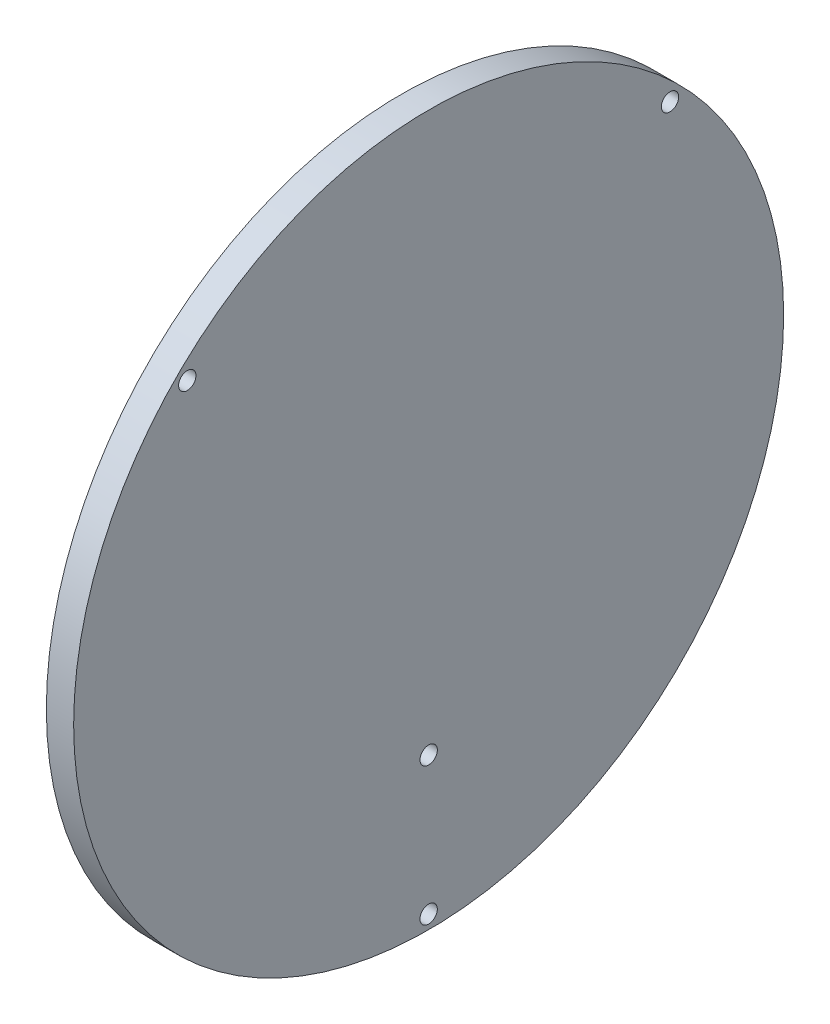
SolidWorks part; units mm, degrees
material "Copper"
ref_plane "Front Plane" through (0, 0, 0) normal (0, 0, 1) x (1, 0, 0)
ref_plane "Top Plane" through (0, 0, 0) normal (0, 1, 0) x (1, 0, 0)
ref_plane "Right Plane" through (0, 0, 0) normal (1, 0, 0) x (0, 0, -1)
sketch "Sketch1" plane through (0, 0, 0) normal (1, 0, 0) x (0, 0, -1)
  circle A0 centre (0, 0) radius 260
extrude "Boss-Extrude1" add sketch "Sketch1" along normal blind 20
ref_plane "Plane1" through (20, 0, 0) normal (1, 0, 0) x (0, 0, -1)
sketch "Sketch2" plane through (20, 0, 0) normal (1, 0, 0) x (0, 0, -1)
  line L0 (0, 260) -> (0, 240)
  line L1 (-260, 0) -> (-240, 0)
  line L2 (183.8478, 183.8478) -> (169.7056, 169.7056)
  line L3 (-183.8478, 183.8478) -> (-169.7056, 169.7056)
  line L4 (169.7056, -169.7056) -> (183.8478, -183.8478)
  line L5 (-169.7056, -169.7056) -> (-183.8478, -183.8478)
  line L6 (0, -240) -> (0, -260)
  line L7 (240, 0) -> (260, 0)
  line L8 (-210.3618, -149.1025) -> (210.3618, -149.1025)
  line L9 (0, 0) -> (0, -149.1025)
  circle A0 centre (0, 3.6977) radius 260
  point P3 (0, -250)
  point P16 (-176.7767, 176.7767)
  point P17 (176.7767, 176.7767)
  point P18 (176.7767, -176.7767)
  point P19 (-176.7767, -176.7767)
hole_wizard "1/2-13 Tapped Hole1" positions "3DSketch1" profile "Sketch3" tap size "1/2-13" standard "ANSI Inch"
sketch3d "3DSketch1"
  point P0 (20, 176.7767, 176.7767)
  point P3 (20, 176.7767, -176.7767)
  point P30 (20, -250, 0)
  point P33 (20, -149.1025, 0)
sketch "Sketch3" plane through (20, 176.7767, 176.7767) normal (0, 1, 0) x (0, 0, -1)
  line L0 (0, 0) -> (0, 73.6195)
  line L1 (0, 73.6195) -> (5.3581, 70.4)
  line L2 (5.3581, 70.4) -> (5.3581, 64.5)
  line L3 (5.3581, 64.5) -> (6.35, 64.5)
  line L4 (6.35, 64.5) -> (6.35, 0)
  line L5 (6.35, 0) -> (0, 0)
  line L10 (0, 73.6195) -> (-5.3581, 70.4) construction
  line L11 (0, -6.35) -> (0, 107.95) construction
  dimension "Tap Drill Dia." = 10.7163
  dimension "Tap Drill Depth" = 70.4
  dimension "Thread Major Dia." = 12.7
  dimension "Thread Depth" = 64.5
  dimension "Drill Angle" = 118
